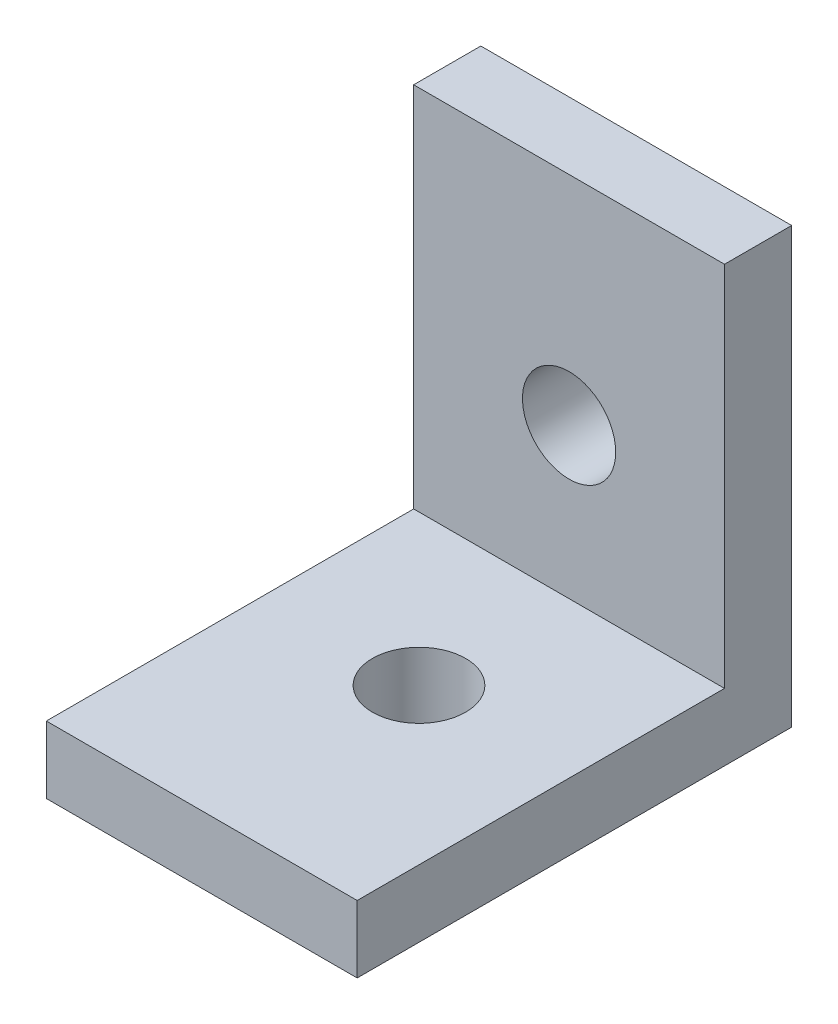
SolidWorks part; units mm, degrees
ref_plane "Front Plane" through (0, 0, 0) normal (0, 0, 1) x (1, 0, 0)
ref_plane "Top Plane" through (0, 0, 0) normal (0, 1, 0) x (1, 0, 0)
ref_plane "Right Plane" through (0, 0, 0) normal (1, 0, 0) x (0, 0, -1)
sketch "Sketch1" plane through (0, 0, 0) normal (0, 1, 0) x (1, 0, 0)
  line L1 (0, 0) -> (19.9898, 0)
  line L2 (0, 0) -> (0, 27.94)
  line L3 (0, 27.94) -> (19.9898, 27.94)
  line L4 (19.9898, 0) -> (19.9898, 27.94)
  dimension "D1" = 27.94
  dimension "D2" = 19.9898
extrude "Boss-Extrude1" add sketch "Sketch1" along normal blind 4.318
sketch "Sketch2" plane through (0, 0, -27.94) normal (0, 0, -1) x (-1, 0, 0)
  line L1 (-19.9898, 0) -> (0, 0)
  line L2 (-19.9898, 0) -> (-19.9898, 27.94)
  line L3 (-19.9898, 27.94) -> (0, 27.94)
  line L4 (0, 0) -> (0, 27.94)
  dimension "D1" = 27.94
extrude "Boss-Extrude2" add sketch "Sketch2" against normal blind 4.318
sketch "Sketch3" plane through (0, 4.318, 0) normal (0, 1, 0) x (1, 0, 0)
  line L0 (0, 23.622) -> (0, 0) construction
  line L1 (0, 0) -> (19.9898, 0) construction
  circle A0 centre (9.9949, 13.97) radius 2.9972
  dimension "D1" = 5.9944
  dimension "D2" = 9.9949
  dimension "D3" = 13.97
sketch "Sketch4" plane through (0, 0, -23.622) normal (0, 0, 1) x (1, 0, 0)
  line L0 (19.9898, 27.94) -> (19.9898, 4.318) construction
  line L1 (0, 27.94) -> (19.9898, 27.94) construction
  circle A0 centre (9.9949, 13.97) radius 2.9972
  dimension "D1" = 5.9944
  dimension "D2" = 9.9949
  dimension "D3" = 13.97
extrude "Cut-Extrude3" cut sketch "Sketch3" against normal through all
extrude "Cut-Extrude4" cut sketch "Sketch4" against normal through all
